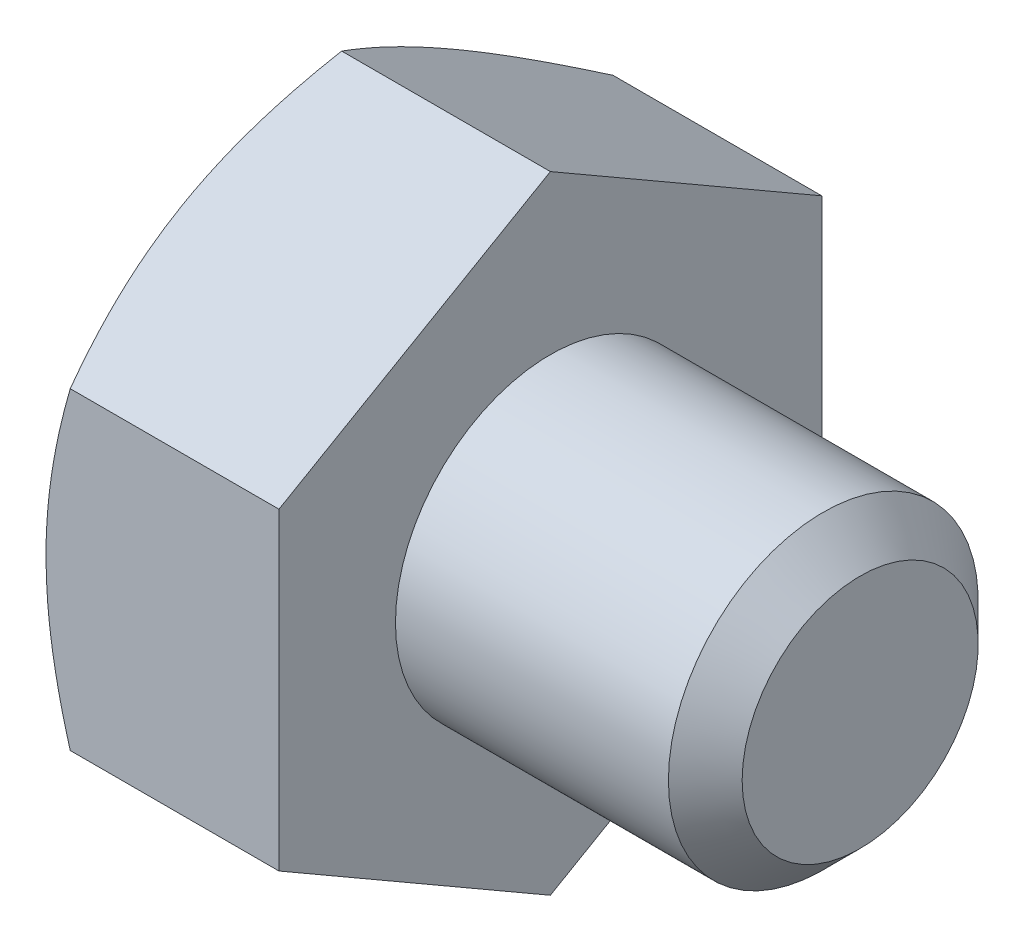
SolidWorks part; units mm, degrees
extrude "BaseHead" add sketch "Sketch1" along normal blind 4.7752
sketch "Sketch1" plane through (0, 0, 0) normal (1, 0, 0) x (0, 0, -1)
  line L0 (5.5626, 3.2116) -> (5.5626, -3.2116)
  line L1 (-5.5626, 3.2116) -> (-5.5626, -3.2116)
  line L2 (5.5626, -3.2116) -> (0, -6.4231)
  line L3 (0, -6.4231) -> (-5.5626, -3.2116)
  line L4 (5.5626, 3.2116) -> (0, 6.4231)
  line L5 (0, 6.4231) -> (-5.5626, 3.2116)
  dimension "Width_flats" = 11.1252
  dimension "D2" = 120
  dimension "D3" = 5.5626
  dimension "D4" = 5.5626
  dimension "D5" = 5.5626
ref_plane "Plane1" through (0, 0, 0) normal (0, 0, 1) x (1, 0, 0)
ref_plane "Plane2" through (0, 0, 0) normal (0, 1, 0) x (1, 0, 0)
ref_plane "Plane3" through (0, 0, 0) normal (1, 0, 0) x (0, 0, -1)
sketch "BodySke" plane through (0, 0, 0) normal (0, 0, 1) x (1, 0, 0)
  line L0 (0, 3.2116) -> (0, -3.2116) construction
  line L1 (0, 0) -> (11.1252, 0)
  line L2 (0, 0) -> (0, 3.175)
  line L3 (0, 3.175) -> (10.3695, 3.175)
  line L4 (11.1252, 0) -> (11.1252, 2.4193)
  line L5 (4.7752, 6.4231) -> (4.7752, 3.2116) construction
  line L6 (11.1252, 2.4193) -> (10.3695, 3.175)
  line L7 (0, 0) -> (96.52, 0) construction
  line L8 (11.1252, -2.4193) -> (10.3695, -3.175) construction
  line L9 (0, -3.175) -> (10.3695, -3.175) construction
  line L10 (6.0452, 15.24) -> (6.0452, -2.54) construction
  line L11 (-4.7498, 15.24) -> (-4.7498, -2.54) construction
  line L12 (4.7752, 3.2116) -> (4.7752, -3.2116) construction
  dimension "Diameter" = 6.35
  dimension "Advance" = 1.27
revolve "BaseBody" add sketch "BodySke" angle 360 about L7
cosmetic thread "ThreadCosmetic" [suppressed] parameters "Thread_length"=5.08, "Thread_minor"=4.8387
sketch "Sketch3" plane through (0, 0, 0) normal (0, 0, 1) x (1, 0, 0)
  line L0 (0, 5.5626) -> (4.163, 12.7731)
  line L1 (0, 6.4231) -> (0, 3.2116) construction
  line L2 (4.163, 12.7731) -> (4.163, 19.1231)
  line L3 (4.163, 19.1231) -> (-12.7, 19.1231)
  line L4 (-12.7, 19.1231) -> (-12.7, 5.5626)
  line L5 (-12.7, 5.5626) -> (0, 5.5626)
  line L6 (0, 0) -> (99.06, 0) construction
  line L7 (4.7752, 6.4231) -> (0, 6.4231) construction
  dimension "D1" = 5.5626
  dimension "D2" = 6.35
  dimension "D3" = 12.7
  dimension "D4" = 6.35
  dimension "Head_ch_ang" = 30
revolve "HeadChamfer" cut sketch "Sketch3" angle 360 about L6
fillet "HeadFillet" [suppressed] radius 0.762
sketch "ThdSchSke" plane through (0, 0, 0) normal (0, 0, 1) x (1, 0, 0)
  line L0 (6.0452, -2.4194) -> (5.5161, -3.175)
  line L1 (6.0452, -2.4194) -> (6.5743, -3.175)
  line L2 (6.5743, -3.175) -> (6.5743, -3.9688)
  line L3 (-3.175, 0) -> (5.1513, 0) construction
  line L5 (6.5743, -3.9688) -> (5.5161, -3.9688)
  line L6 (5.5161, -3.9688) -> (5.5161, -3.175)
  dimension "Thread_minor" = 4.8387
  dimension "Diameter" = 6.35
  dimension "Start" = 6.0452
revolve "ThreadSchematic" [suppressed] cut sketch "ThdSchSke" angle 360 about L3
pattern_linear "ThdSchPat" [suppressed]
equation "\"D3@Sketch1\" = \"Width_flats@Sketch1\" / 2"
equation "\"D4@Sketch1\" = \"D3@Sketch1\""
equation "\"D5@Sketch1\" = \"D4@Sketch1\""
equation "\"Thread_minor@ThreadCosmetic\" = \"Minor_dia@BodySke\""
equation "\"D1@Sketch3\" = \"Width_flats@Sketch1\" / 2"
equation "\"Thread_length@ThreadCosmetic\" = ((sgn( (\"Length@BodySke\" - \"Advance@BodySke\" ) - \"Thread_nom@BodySke\" )-1)*( (\"Length@BodySke\" - \"Advance@BodySke\" ) - \"Thread_nom@BodySke\" ))/-2+ \"Thread_nom@BodySke\""
equation "\"Thread_minor@ThdSchSke\" = \"Minor_dia@BodySke\""
equation "\"Diameter@ThdSchSke\" = \"Diameter@BodySke\""
equation "\"Overcut@ThdSchSke\" = \"Diameter@BodySke\" * 1.25"
equation "\"Start@ThdSchSke\" = \"Head_ht@BaseHead\" + \"Length@BodySke\" - \"Thread_length@ThreadCosmetic\"  '---Non-countersunk---"
equation "\"Num_threads@ThdSchPat\" = int( \"Thread_length@ThreadCosmetic\" / \"Advance@BodySke\" + 0.999 )  + 1"
equation "\"Advance@ThdSchPat\" = \"Thread_length@ThreadCosmetic\" /  (\"Num_threads@ThdSchPat\" - 1) 'relax it"
equation "\"Num_threads@ThdSchPat\" = \"Num_threads@ThdSchPat\" - sgn( \"Num_threads@ThdSchPat\" - 1) '---chamfered tips only---"
